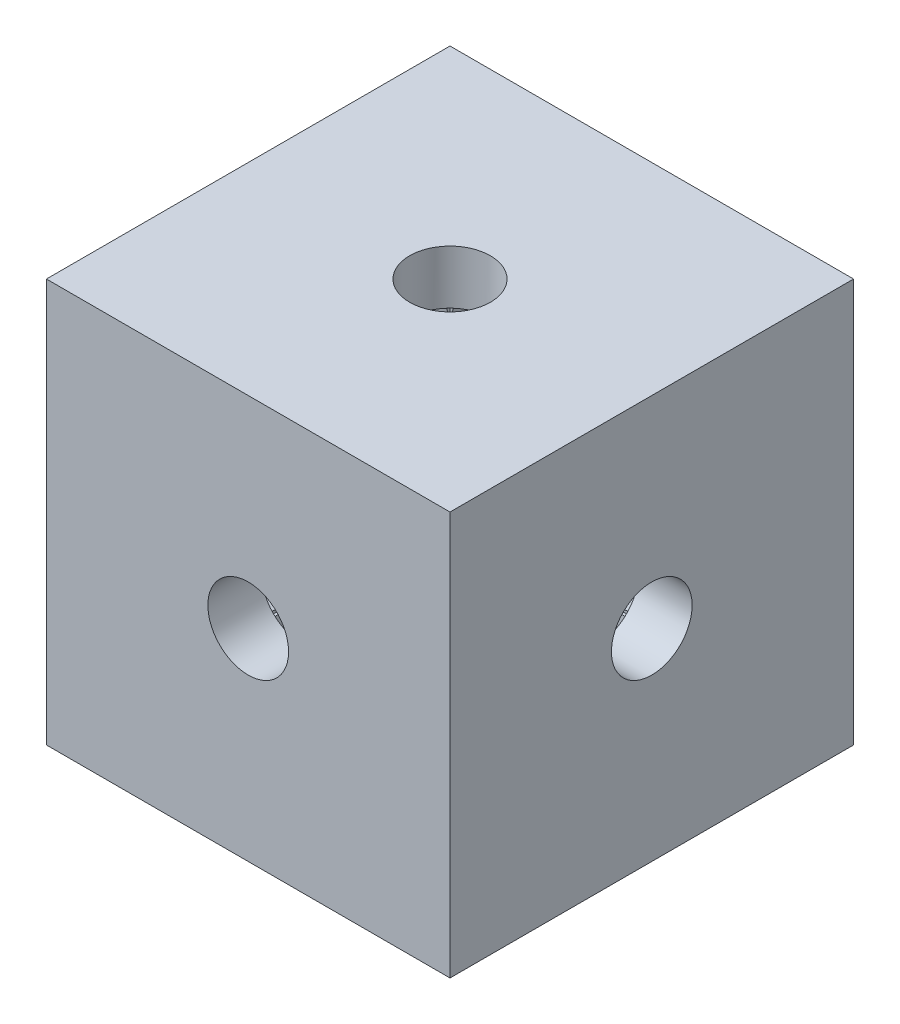
SolidWorks part; units mm, degrees
ref_plane "Front Plane" through (0, 0, 0) normal (0, 0, 1) x (1, 0, 0)
ref_plane "Top Plane" through (0, 0, 0) normal (0, 1, 0) x (1, 0, 0)
ref_plane "Right Plane" through (0, 0, 0) normal (1, 0, 0) x (0, 0, -1)
sketch "Sketch1" plane through (0, 0, 0) normal (0, 1, 0) x (1, 0, 0)
  line L1 (-7.5, -7.5) -> (7.5, -7.5)
  line L2 (-7.5, -7.5) -> (-7.5, 7.5)
  line L3 (-7.5, 7.5) -> (7.5, 7.5)
  line L4 (7.5, -7.5) -> (7.5, 7.5)
  line L5 (-7.5, -7.5) -> (7.5, 7.5) construction
  line L6 (-7.5, 7.5) -> (7.5, -7.5) construction
  line L7 (5.5, -5.5) -> (-5.5, -5.5)
  line L8 (5.5, -5.5) -> (5.5, 5.5)
  line L9 (5.5, 5.5) -> (-5.5, 5.5)
  line L10 (-5.5, -5.5) -> (-5.5, 5.5)
  line L11 (5.5, -5.5) -> (-5.5, 5.5) construction
  line L12 (5.5, 5.5) -> (-5.5, -5.5) construction
  point P0 (0, 0)
  point P5 (0, 0)
  dimension "D1" = 15
  dimension "D2" = 2
extrude "Boss-Extrude1" add sketch "Sketch1" along normal blind 2
sketch "Sketch5" plane through (0, 2, 0) normal (0, 1, 0) x (1, 0, 0)
  line L1 (-7.5, -7.5) -> (-5.5, -7.5)
  line L2 (-7.5, -7.5) -> (-7.5, -5.5)
  line L3 (-7.5, -5.5) -> (-5.5, -5.5)
  line L4 (-5.5, -7.5) -> (-5.5, -5.5)
  line L5 (7.5, -7.5) -> (5.5, -7.5)
  line L6 (7.5, -7.5) -> (7.5, -5.5)
  line L7 (7.5, -5.5) -> (5.5, -5.5)
  line L8 (5.5, -7.5) -> (5.5, -5.5)
  line L9 (7.5, 7.5) -> (5.5, 7.5)
  line L10 (7.5, 7.5) -> (7.5, 5.5)
  line L11 (7.5, 5.5) -> (5.5, 5.5)
  line L12 (5.5, 7.5) -> (5.5, 5.5)
  line L13 (-7.5, 7.5) -> (-5.5, 7.5)
  line L14 (-7.5, 7.5) -> (-7.5, 5.5)
  line L15 (-7.5, 5.5) -> (-5.5, 5.5)
  line L16 (-5.5, 7.5) -> (-5.5, 5.5)
extrude "Boss-Extrude2" add sketch "Sketch5" along normal blind 11
sketch "Sketch8" plane through (0, 13, 0) normal (0, 1, 0) x (1, 0, 0)
  line L0 (-7.5, -7.5) -> (-7.5, 7.5)
  line L1 (-7.5, 7.5) -> (7.5, 7.5)
  line L2 (7.5, 7.5) -> (7.5, -7.5)
  line L3 (5.5, -7.5) -> (7.5, -7.5) construction
  line L4 (7.5, -7.5) -> (7.5, -5.5) construction
  line L5 (7.5, -7.5) -> (-7.5, -7.5)
  line L7 (-5.5, -5.5) -> (5.5, -5.5)
  line L8 (-5.5, -5.5) -> (-5.5, 5.5)
  line L9 (-5.5, 5.5) -> (5.5, 5.5)
  line L10 (5.5, -5.5) -> (5.5, 5.5)
extrude "Boss-Extrude3" add sketch "Sketch8" along normal blind 2
sketch "Sketch9" plane through (0, 0, 0) normal (0, -1, 0) x (1, 0, 0)
  line L0 (7.5, 0) -> (-7.5, 0) construction
  line L1 (7.5, 7.5) -> (7.5, -7.5) construction
  line L2 (-7.5, -7.5) -> (-7.5, 7.5) construction
  line L4 (5.5, 5.5) -> (-5.5, 5.5)
  line L5 (5.5, 5.5) -> (5.5, -5.5)
  line L6 (5.5, -5.5) -> (-5.5, -5.5)
  line L7 (-5.5, 5.5) -> (-5.5, -5.5)
  circle A0 centre (0, 0) radius 5.5
  line M6 (5.5, -5.5) -> (-5.5, -5.5)
  line M7 (-5.5, -5.5) -> (-5.5, 5.5)
  line M8 (-5.5, 5.5) -> (5.5, 5.5)
  line M9 (5.5, 5.5) -> (5.5, -5.5)
extrude "Boss-Extrude4" add sketch "Sketch9" against normal up to surface (2 mm away) contours A0 L4 M9 | A0 L7 M8 | A0 L5 M6 | A0 L6 M7 up to face at (0, 2, 6.5)
sketch "Sketch10" plane through (0, 0, -7.5) normal (0, 0, -1) x (-1, 0, 0)
  line L0 (0, 0) -> (0, 15) construction
  line L1 (-7.5, 0) -> (7.5, 0) construction
  line L2 (-7.5, 15) -> (7.5, 15) construction
  line L4 (-5.5, 2) -> (5.5, 2)
  line L5 (-5.5, 2) -> (-5.5, 13)
  line L6 (-5.5, 13) -> (5.5, 13)
  line L7 (5.5, 2) -> (5.5, 13)
  circle A0 centre (0, 7.5) radius 5.5
  line M2 (-5.5, 2) -> (-5.5, 13)
  line M3 (-5.5, 13) -> (5.5, 13)
  line M4 (5.5, 13) -> (5.5, 2)
  line M5 (5.5, 2) -> (-5.5, 2)
extrude "Boss-Extrude5" add sketch "Sketch10" against normal up to surface (2 mm away) contours A0 L5 M3 | A0 L6 M4 | A0 L7 M5 | A0 L4 M2 up to face at (6.5, 7.5, -5.5)
sketch "Sketch11" plane through (-7.5, 0, 0) normal (-1, 0, 0) x (0, 0, 1)
  line L0 (0, 2) -> (0, 13) construction
  line L1 (-5.5, 2) -> (5.5, 2) construction
  line L2 (-5.5, 13) -> (5.5, 13) construction
  line L3 (-5.5, 13) -> (-5.5, 2) construction
  line L4 (-5.5, 2) -> (5.5, 2)
  line L5 (-5.5, 2) -> (-5.5, 13)
  line L6 (-5.5, 13) -> (5.5, 13)
  line L7 (5.5, 2) -> (5.5, 13)
  circle A0 centre (0, 7.5) radius 5.5
  line M6 (-5.5, 13) -> (5.5, 13)
  line M7 (5.5, 13) -> (5.5, 2)
  line M8 (5.5, 2) -> (-5.5, 2)
  line M9 (-5.5, 2) -> (-5.5, 13)
extrude "Boss-Extrude6" add sketch "Sketch11" against normal up to surface (2 mm away) contours A0 L5 M6 | A0 L6 M7 | A0 L4 M9 | A0 L7 M8 up to face at (-5.5, 7.5, 6.5)
sketch "Sketch12" plane through (0, 0, 7.5) normal (0, 0, 1) x (1, 0, 0)
  line L0 (0, 2) -> (0, 13) construction
  line L1 (-5.5, 2) -> (5.5, 2)
  line L2 (-5.5, 2) -> (-5.5, 13)
  line L3 (-5.5, 13) -> (5.5, 13)
  line L4 (5.5, 2) -> (5.5, 13)
  circle A0 centre (0, 7.5) radius 1.5
  dimension "D1" = 3
extrude "Boss-Extrude7" add sketch "Sketch12" against normal up to surface (2 mm away) up to face at (6.5, 7.5, 5.5)
sketch "Sketch13" plane through (0, 15, 0) normal (0, 1, 0) x (1, 0, 0)
  line L0 (-5.5, 0) -> (5.5, 0) construction
  line L1 (-5.5, 5.5) -> (-5.5, -5.5) construction
  line L2 (5.5, -5.5) -> (5.5, 5.5) construction
  line L4 (-5.5, 5.5) -> (5.5, 5.5)
  line L5 (-5.5, 5.5) -> (-5.5, -5.5)
  line L6 (-5.5, -5.5) -> (5.5, -5.5)
  line L7 (5.5, 5.5) -> (5.5, -5.5)
  circle A0 centre (0, 0) radius 1.5
  dimension "D1" = 3
extrude "Boss-Extrude8" add sketch "Sketch13" against normal up to surface (2 mm away) up to face at (6.5, 13, 0)
sketch "Sketch14" plane through (7.5, 0, 0) normal (1, 0, 0) x (0, 0, -1)
  line L0 (0, 2) -> (0, 13) construction
  line L1 (-5.5, 2) -> (5.5, 2) construction
  line L2 (-5.5, 13) -> (5.5, 13) construction
  line L4 (-5.5, 2) -> (5.5, 2)
  line L5 (-5.5, 2) -> (-5.5, 13)
  line L6 (-5.5, 13) -> (5.5, 13)
  line L7 (5.5, 2) -> (5.5, 13)
  circle A0 centre (0, 7.5) radius 1.5
  dimension "D1" = 3
extrude "Boss-Extrude9" add sketch "Sketch14" against normal up to vertex (2.2085 mm away)
